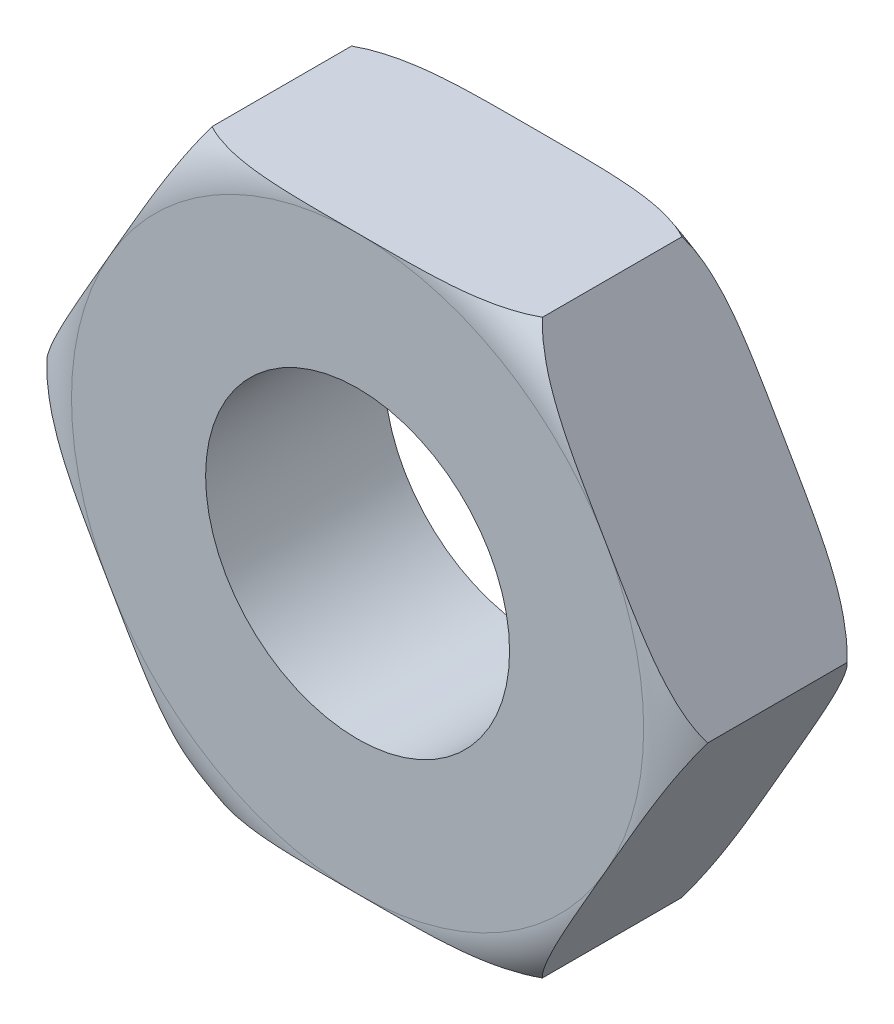
SolidWorks part; units mm, degrees
ref_plane "Plan de face" through (0, 0, 0) normal (0, 0, 1) x (1, 0, 0)
ref_plane "Plan de dessus" through (0, 0, 0) normal (0, 1, 0) x (1, 0, 0)
ref_plane "Plan de droite" through (0, 0, 0) normal (1, 0, 0) x (0, 0, -1)
sketch "Esquisse1" plane through (0, 0, 0) normal (0, 0, 1) x (1, 0, 0)
  line L1 (-4.6188, -8) -> (4.6188, -8)
  line L2 (4.6188, -8) -> (9.2376, 0)
  line L3 (9.2376, 0) -> (4.6188, 8)
  line L4 (4.6188, 8) -> (-4.6188, 8)
  line L5 (-4.6188, 8) -> (-9.2376, 0)
  line L6 (-9.2376, 0) -> (-4.6188, -8)
  circle A0 centre (0, 0) radius 8 construction
  circle A1 centre (0, 0) radius 4.25
  point P10 (-4.3733, -7.8558)
  dimension "D2" = 8.5
  dimension "D1" = 16
extrude "Boss.-Extru.1" add sketch "Esquisse1" along normal mid plane 5
cosmetic thread "Représentation de filetage1" parameters "D1"=5, "D2"=10
sketch "Esquisse3" plane through (0, 0, 0) normal (1, 0, 0) x (0, 0, -1)
  line L5 (-5.6171, 0) -> (6.6034, 0) construction
  line L6 (-2.5, 8) -> (2.5, 8) construction
  line L8 (3, 10.1014) -> (3, 8)
  line L9 (3, 8) -> (2.5, 8)
  line L10 (2.5, 0) -> (2.5, 8) construction
  line L11 (1.3, 9.6014) -> (1.3, 10.1014)
  line L12 (1.3, 10.1014) -> (3, 10.1014)
  arc A1 (2.5, 8) -> (1.3, 9.6014) centre (0.8314, 8) ccw
  point P3 (3.0841, 10.0078)
  point P14 (0, 0)
  point P15 (3, 10.111)
  dimension "D1" = 1.6686
  dimension "D2" = 0.5
  dimension "D3" = 0.5
  dimension "D4" = 1.7
revolve "Enlèvement de matière-Révolution2" cut sketch "Esquisse3" angle 360 about L5
mirror "Symétrie1" about plane through (0, 0, 0) normal (0, 0, 1) of "Enlèvement de matière-Révolution2"
